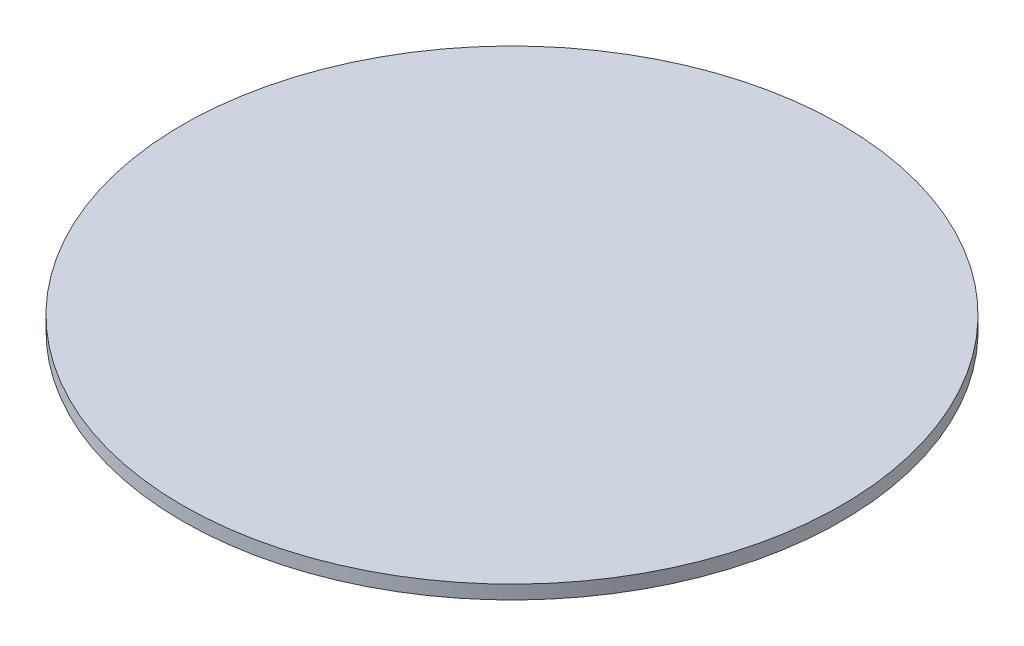
SolidWorks part; units mm, degrees
ref_plane "Front" through (0, 0, 0) normal (0, 0, 1) x (1, 0, 0)
ref_plane "Top" through (0, 0, 0) normal (0, 1, 0) x (1, 0, 0)
ref_plane "Right" through (0, 0, 0) normal (1, 0, 0) x (0, 0, -1)
sketch "Record Sketch" plane through (0, 0, 0) normal (0, 1, 0) x (1, 0, 0)
  circle A0 centre (0, 0) radius 76.2
  dimension "D1" = 152.4
extrude "Record" add sketch "Record Sketch" along normal blind 3.175
